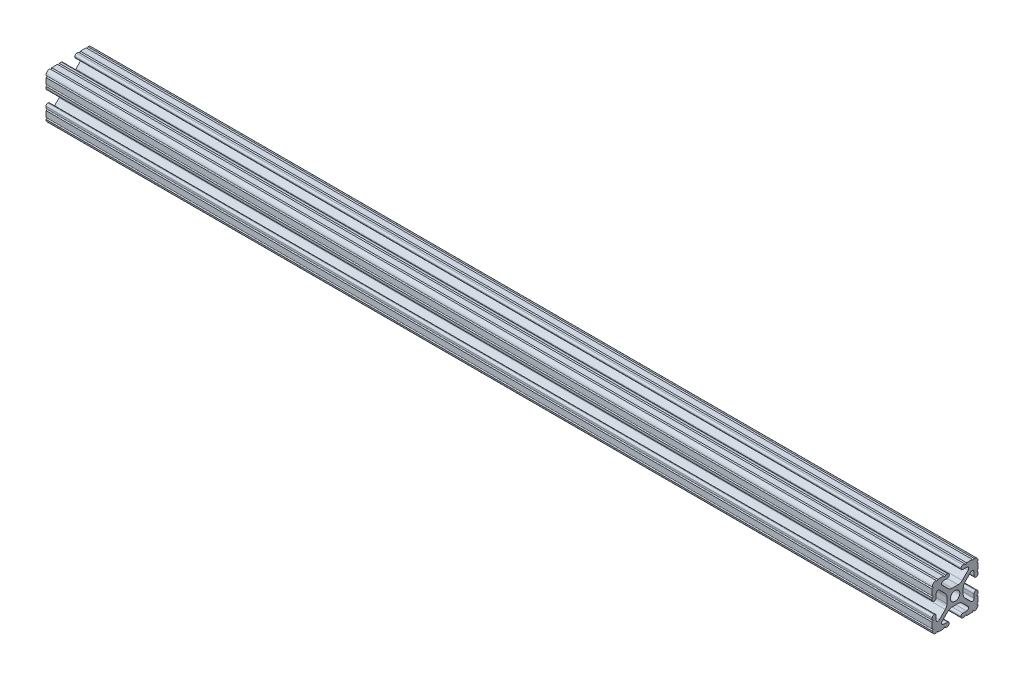
SolidWorks part; units mm, degrees
ref_plane "Front Plane" through (0, 0, 0) normal (0, 0, 1) x (1, 0, 0)
ref_plane "Top Plane" through (0, 0, 0) normal (0, 1, 0) x (1, 0, 0)
ref_plane "Right Plane" through (0, 0, 0) normal (1, 0, 0) x (0, 0, -1)
sketch "Sketch1" plane through (0, 0, 0) normal (0, 1, 0) x (1, 0, 0)
  line L0 (0, 0) -> (-491.49, 0)
  dimension "D1" = 491.49
other "10 1010 PROFILE(1)"
ref_plane "Plane1" through (0, 0, 0) normal (-1, 0, 0) x (0, 0, 1)
sketch "Sketch14" plane through (0, 0, 0) normal (-1, 0, 0) x (0, 0, 1)
  line L1 (12.7, 12.7) -> (-12.7, 12.7) construction
  line L2 (12.7, 12.7) -> (12.7, -12.7) construction
  line L3 (12.7, -12.7) -> (-12.7, -12.7) construction
  line L4 (-12.7, 12.7) -> (-12.7, -12.7) construction
  line L5 (12.7, 12.7) -> (-12.7, -12.7) construction
  line L6 (12.7, -12.7) -> (-12.7, 12.7) construction
  line L88 (-1.7093, -4.4958) -> (1.7093, -4.4958)
  line L89 (3.9523, -5.4237) -> (7.1797, -8.6452)
  line L90 (6.4164, -10.4902) -> (4.2875, -10.4902)
  line L91 (3.2385, -11.5392) -> (3.2385, -11.651)
  line L92 (4.2875, -12.7) -> (5.3171, -12.7)
  line L93 (6.3331, -12.7) -> (9.5504, -12.7)
  line L94 (12.7, -9.5504) -> (12.7, -6.3331)
  line L95 (12.7, -5.3171) -> (12.7, -4.2875)
  line L96 (11.651, -3.2385) -> (11.5392, -3.2385)
  line L97 (10.4902, -4.2875) -> (10.4902, -6.4021)
  line L98 (8.737, -7.1292) -> (5.4405, -3.8388)
  line L99 (4.5085, -1.5917) -> (4.5085, 1.5917)
  line L100 (5.4405, 3.8388) -> (8.737, 7.1292)
  line L101 (10.4902, 6.4021) -> (10.4902, 4.2875)
  line L102 (11.5392, 3.2385) -> (11.651, 3.2385)
  line L103 (12.7, 4.2875) -> (12.7, 5.3171)
  line L104 (12.7, 6.3331) -> (12.7, 9.5504)
  line L105 (9.5504, 12.7) -> (6.3331, 12.7)
  line L106 (5.3171, 12.7) -> (4.2875, 12.7)
  line L107 (3.2384, 11.651) -> (3.2384, 11.5392)
  line L108 (4.2875, 10.4902) -> (6.4768, 10.4902)
  line L109 (7.2072, 8.7245) -> (3.9003, 5.4237)
  line L110 (1.6573, 4.4958) -> (-1.6573, 4.4958)
  line L111 (-3.9003, 5.4237) -> (-7.2072, 8.7245)
  line L112 (-6.4768, 10.4902) -> (-4.2875, 10.4902)
  line L113 (-3.2384, 11.5392) -> (-3.2384, 11.651)
  line L114 (-4.2875, 12.7) -> (-5.3171, 12.7)
  line L115 (-6.3331, 12.7) -> (-9.5504, 12.7)
  line L116 (-12.7, 9.5504) -> (-12.7, 6.3331)
  line L117 (-12.7, 5.3171) -> (-12.7, 4.2875)
  line L118 (-11.651, 3.2385) -> (-11.5392, 3.2385)
  line L119 (-10.4902, 4.2875) -> (-10.4902, 6.4021)
  line L120 (-8.737, 7.1292) -> (-5.4405, 3.8388)
  line L121 (-4.5085, 1.5917) -> (-4.5085, -1.5917)
  line L122 (-5.4405, -3.8388) -> (-8.737, -7.1292)
  line L123 (-10.4902, -6.4021) -> (-10.4902, -4.2875)
  line L124 (-11.5392, -3.2385) -> (-11.651, -3.2385)
  line L125 (-12.7, -4.2875) -> (-12.7, -5.3171)
  line L126 (-12.7, -6.3331) -> (-12.7, -9.5504)
  line L127 (-9.5504, -12.7) -> (-6.3331, -12.7)
  line L128 (-5.3171, -12.7) -> (-4.2875, -12.7)
  line L129 (-3.2385, -11.651) -> (-3.2385, -11.5392)
  line L130 (-4.2875, -10.4902) -> (-6.4164, -10.4902)
  line L131 (-7.1797, -8.6452) -> (-3.9523, -5.4237)
  circle A1 centre (0, 0) radius 2.6035
  arc A104 (-1.7093, -4.4958) -> (-3.9523, -5.4237) centre (-1.7093, -7.6708) ccw
  arc A105 (3.9523, -5.4237) -> (1.7093, -4.4958) centre (1.7093, -7.6708) ccw
  arc A106 (6.4164, -10.4902) -> (7.1797, -8.6452) centre (6.4164, -9.4098) ccw
  arc A107 (4.2875, -10.4902) -> (3.2385, -11.5392) centre (4.2875, -11.5392) ccw
  arc A108 (3.2385, -11.651) -> (4.2875, -12.7) centre (4.2875, -11.651) ccw
  arc A109 (6.3331, -12.7) -> (5.3171, -12.7) centre (5.8251, -12.7) ccw
  arc A110 (10.5664, -12.6998) -> (9.5504, -12.7) centre (10.0584, -12.7) ccw
  arc A111 (10.5664, -12.6998) -> (12.6998, -10.5664) centre (10.5918, -10.5918) ccw
  arc A112 (12.7, -9.5504) -> (12.6998, -10.5664) centre (12.7, -10.0584) ccw
  arc A113 (12.7, -5.3171) -> (12.7, -6.3331) centre (12.7, -5.8251) ccw
  arc A114 (12.7, -4.2875) -> (11.651, -3.2385) centre (11.651, -4.2875) ccw
  arc A115 (11.5392, -3.2385) -> (10.4902, -4.2875) centre (11.5392, -4.2875) ccw
  arc A116 (8.737, -7.1292) -> (10.4902, -6.4021) centre (9.4628, -6.4021) ccw
  arc A117 (4.5085, -1.5917) -> (5.4405, -3.8388) centre (7.6835, -1.5917) ccw
  arc A118 (5.4405, 3.8388) -> (4.5085, 1.5917) centre (7.6835, 1.5917) ccw
  arc A119 (10.4902, 6.4021) -> (8.737, 7.1292) centre (9.4628, 6.4021) ccw
  arc A120 (10.4902, 4.2875) -> (11.5392, 3.2385) centre (11.5392, 4.2875) ccw
  arc A121 (11.651, 3.2385) -> (12.7, 4.2875) centre (11.651, 4.2875) ccw
  arc A122 (12.7, 6.3331) -> (12.7, 5.3171) centre (12.7, 5.8251) ccw
  arc A123 (12.6998, 10.5664) -> (12.7, 9.5504) centre (12.7, 10.0584) ccw
  arc A124 (12.6998, 10.5664) -> (10.5664, 12.6998) centre (10.5918, 10.5918) ccw
  arc A125 (9.5504, 12.7) -> (10.5664, 12.6998) centre (10.0584, 12.7) ccw
  arc A126 (5.3171, 12.7) -> (6.3331, 12.7) centre (5.8251, 12.7) ccw
  arc A127 (4.2875, 12.7) -> (3.2384, 11.651) centre (4.2875, 11.651) ccw
  arc A128 (3.2384, 11.5392) -> (4.2875, 10.4902) centre (4.2875, 11.5392) ccw
  arc A129 (7.2072, 8.7245) -> (6.4768, 10.4902) centre (6.4768, 9.4563) ccw
  arc A130 (1.6573, 4.4958) -> (3.9003, 5.4237) centre (1.6573, 7.6708) ccw
  arc A131 (-3.9003, 5.4237) -> (-1.6573, 4.4958) centre (-1.6573, 7.6708) ccw
  arc A132 (-6.4768, 10.4902) -> (-7.2072, 8.7245) centre (-6.4768, 9.4563) ccw
  arc A133 (-4.2875, 10.4902) -> (-3.2384, 11.5392) centre (-4.2875, 11.5392) ccw
  arc A134 (-3.2384, 11.651) -> (-4.2875, 12.7) centre (-4.2875, 11.651) ccw
  arc A135 (-6.3331, 12.7) -> (-5.3171, 12.7) centre (-5.8251, 12.7) ccw
  arc A136 (-10.5664, 12.6998) -> (-9.5504, 12.7) centre (-10.0584, 12.7) ccw
  arc A137 (-10.5664, 12.6998) -> (-12.6998, 10.5664) centre (-10.5918, 10.5918) ccw
  arc A138 (-12.7, 9.5504) -> (-12.6998, 10.5664) centre (-12.7, 10.0584) ccw
  arc A139 (-12.7, 5.3171) -> (-12.7, 6.3331) centre (-12.7, 5.8251) ccw
  arc A140 (-12.7, 4.2875) -> (-11.651, 3.2385) centre (-11.651, 4.2875) ccw
  arc A141 (-11.5392, 3.2385) -> (-10.4902, 4.2875) centre (-11.5392, 4.2875) ccw
  arc A142 (-8.737, 7.1292) -> (-10.4902, 6.4021) centre (-9.4628, 6.4021) ccw
  arc A143 (-4.5085, 1.5917) -> (-5.4405, 3.8388) centre (-7.6835, 1.5917) ccw
  arc A144 (-5.4405, -3.8388) -> (-4.5085, -1.5917) centre (-7.6835, -1.5917) ccw
  arc A145 (-10.4902, -6.4021) -> (-8.737, -7.1292) centre (-9.4628, -6.4021) ccw
  arc A146 (-10.4902, -4.2875) -> (-11.5392, -3.2385) centre (-11.5392, -4.2875) ccw
  arc A147 (-11.651, -3.2385) -> (-12.7, -4.2875) centre (-11.651, -4.2875) ccw
  arc A148 (-12.7, -6.3331) -> (-12.7, -5.3171) centre (-12.7, -5.8251) ccw
  arc A149 (-12.6998, -10.5664) -> (-12.7, -9.5504) centre (-12.7, -10.0584) ccw
  arc A150 (-12.6998, -10.5664) -> (-10.5664, -12.6998) centre (-10.5918, -10.5918) ccw
  arc A151 (-9.5504, -12.7) -> (-10.5664, -12.6998) centre (-10.0584, -12.7) ccw
  arc A152 (-5.3171, -12.7) -> (-6.3331, -12.7) centre (-5.8251, -12.7) ccw
  arc A153 (-4.2875, -12.7) -> (-3.2385, -11.651) centre (-4.2875, -11.651) ccw
  arc A154 (-3.2385, -11.5392) -> (-4.2875, -10.4902) centre (-4.2875, -11.5392) ccw
  arc A155 (-7.1797, -8.6452) -> (-6.4164, -10.4902) centre (-6.4164, -9.4098) ccw
  point P3 (0, 0)
  point P21 (-12.7, 0)
  point P22 (0, 12.7)
  point P25 (12.7, 0)
  point P28 (0, -12.7)
  point P30 (-12.7, -12.7)
  point P33 (12.7, -12.7)
  point P37 (12.7, 12.7)
  point P40 (-12.7, 12.7)
  point P43 (0, 0)
  dimension "D1" = 25.4
